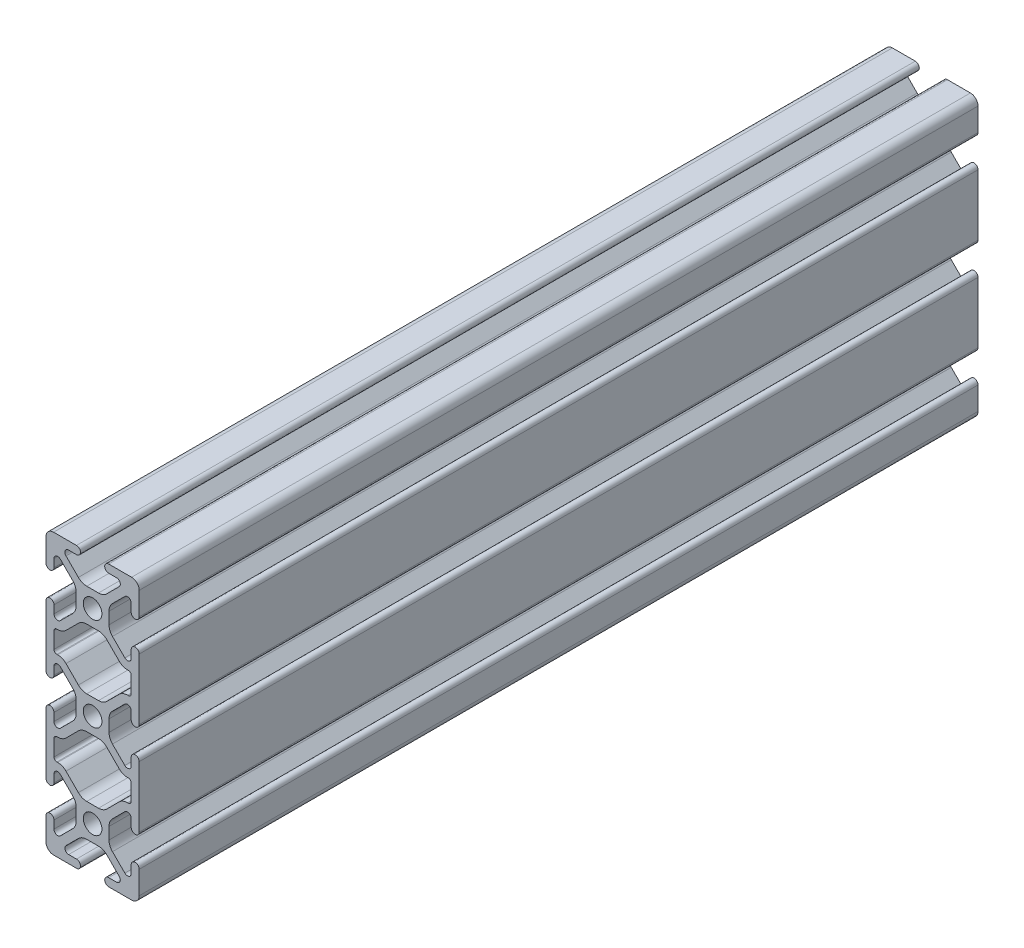
SolidWorks part; units mm, degrees
ref_plane "Front Plane" through (0, 0, 0) normal (0, 0, 1) x (1, 0, 0)
ref_plane "Top Plane" through (0, 0, 0) normal (0, 1, 0) x (1, 0, 0)
ref_plane "Right Plane" through (0, 0, 0) normal (1, 0, 0) x (0, 0, -1)
ref_plane "Plane1" through (0, 0, -225) normal (0, 0, -1) x (-1, 0, 0)
sketch "Sketch1" plane through (0, 0, -225) normal (0, 0, -1) x (-1, 0, 0)
  line L0 (10.36, -10.33) -> (10.36, -14.67)
  line L1 (9.6, -15.43) -> (9.3582, -15.43)
  line L2 (7.1366, -16.3502) -> (3.8153, -19.6715)
  line L3 (1.5737, -20.6) -> (-1.5737, -20.6)
  line L4 (-3.8153, -19.6715) -> (-7.1366, -16.3502)
  line L5 (-9.3582, -15.43) -> (-9.6, -15.43)
  line L6 (-10.36, -14.67) -> (-10.36, -10.33)
  line L7 (-9.6, -9.57) -> (-9.3582, -9.57)
  line L8 (-7.1366, -8.6498) -> (-3.8153, -5.3285)
  line L9 (-1.5737, -4.4) -> (1.5737, -4.4)
  line L10 (3.8153, -5.3285) -> (7.1366, -8.6498)
  line L11 (9.3582, -9.57) -> (9.6, -9.57)
  line L12 (10.36, 14.67) -> (10.36, 10.33)
  line L13 (9.6, 9.57) -> (9.3582, 9.57)
  line L14 (7.1366, 8.6498) -> (3.8153, 5.3285)
  line L15 (1.5737, 4.4) -> (-1.5737, 4.4)
  line L16 (-3.8153, 5.3285) -> (-7.1366, 8.6498)
  line L17 (-9.3582, 9.57) -> (-9.6, 9.57)
  line L18 (-10.36, 10.33) -> (-10.36, 14.67)
  line L19 (-9.6, 15.43) -> (-9.3582, 15.43)
  line L20 (-7.1366, 16.3502) -> (-3.8153, 19.6715)
  line L21 (-1.5737, 20.6) -> (1.5737, 20.6)
  line L22 (3.8153, 19.6715) -> (7.1366, 16.3502)
  line L23 (9.3582, 15.43) -> (9.6, 15.43)
  line L24 (10.36, -29.32) -> (10.36, -31.4282)
  line L25 (8.6498, -32.1366) -> (5.3285, -28.8153)
  line L26 (4.4, -26.5737) -> (4.4, -23.4263)
  line L27 (5.3285, -21.1847) -> (8.6498, -17.8634)
  line L28 (10.36, -18.5718) -> (10.36, -20.68)
  line L29 (12.5, -20.68) -> (12.5, -4.32)
  line L30 (10.36, -4.32) -> (10.36, -6.4282)
  line L31 (8.6498, -7.1366) -> (5.3285, -3.8153)
  line L32 (4.4, -1.5737) -> (4.4, 1.5737)
  line L33 (5.3285, 3.8153) -> (8.6498, 7.1366)
  line L34 (10.36, 6.4282) -> (10.36, 4.32)
  line L35 (12.5, 4.32) -> (12.5, 20.68)
  line L36 (10.36, 20.68) -> (10.36, 18.5718)
  line L37 (8.6498, 17.8634) -> (5.3285, 21.1847)
  line L38 (4.4, 23.4263) -> (4.4, 26.5737)
  line L39 (5.3285, 28.8153) -> (8.6498, 32.1366)
  line L40 (10.36, 31.4282) -> (10.36, 29.32)
  line L41 (12.5, 29.32) -> (12.5, 35.469)
  line L42 (10.469, 37.5) -> (4.32, 37.5)
  line L43 (4.32, 35.36) -> (6.4282, 35.36)
  line L44 (7.1366, 33.6498) -> (3.8153, 30.3285)
  line L45 (1.5737, 29.4) -> (-1.5737, 29.4)
  line L46 (-3.8153, 30.3285) -> (-7.1366, 33.6498)
  line L47 (-6.4282, 35.36) -> (-4.32, 35.36)
  line L48 (-4.32, 37.5) -> (-10.469, 37.5)
  line L49 (-12.5, 35.469) -> (-12.5, 29.32)
  line L50 (-10.36, 29.32) -> (-10.36, 31.4282)
  line L51 (-8.6498, 32.1366) -> (-5.3285, 28.8153)
  line L52 (-4.4, 26.5737) -> (-4.4, 23.4263)
  line L53 (-5.3285, 21.1847) -> (-8.6498, 17.8634)
  line L54 (-10.36, 18.5718) -> (-10.36, 20.68)
  line L55 (-12.5, 20.68) -> (-12.5, 4.32)
  line L56 (-10.36, 4.32) -> (-10.36, 6.4282)
  line L57 (-8.6498, 7.1366) -> (-5.3285, 3.8153)
  line L58 (-4.4, 1.5737) -> (-4.4, -1.5737)
  line L59 (-5.3285, -3.8153) -> (-8.6498, -7.1366)
  line L60 (-10.36, -6.4282) -> (-10.36, -4.32)
  line L61 (-12.5, -4.32) -> (-12.5, -20.68)
  line L62 (-10.36, -20.68) -> (-10.36, -18.5718)
  line L63 (-8.6498, -17.8634) -> (-5.3285, -21.1847)
  line L64 (-4.4, -23.4263) -> (-4.4, -26.5737)
  line L65 (-5.3285, -28.8153) -> (-8.6498, -32.1366)
  line L66 (-10.36, -31.4282) -> (-10.36, -29.32)
  line L67 (-12.5, -29.32) -> (-12.5, -35.469)
  line L68 (-10.469, -37.5) -> (-4.32, -37.5)
  line L69 (-4.32, -35.36) -> (-6.4282, -35.36)
  line L70 (-7.1366, -33.6498) -> (-3.8153, -30.3285)
  line L71 (-1.5737, -29.4) -> (1.5737, -29.4)
  line L72 (3.8153, -30.3285) -> (7.1366, -33.6498)
  line L73 (6.4282, -35.36) -> (4.32, -35.36)
  line L74 (4.32, -37.5) -> (10.469, -37.5)
  line L75 (12.5, -35.469) -> (12.5, -29.32)
  arc A0 (9.6, -9.57) -> (10.36, -10.33) centre (9.6, -10.33) cw
  arc A1 (10.36, -14.67) -> (9.6, -15.43) centre (9.6, -14.67) cw
  arc A2 (9.3582, -15.43) -> (7.1366, -16.3502) centre (9.3582, -18.5718) ccw
  arc A3 (3.8153, -19.6715) -> (1.5737, -20.6) centre (1.5737, -17.43) cw
  arc A4 (-1.5737, -20.6) -> (-3.8153, -19.6715) centre (-1.5737, -17.43) cw
  arc A5 (-7.1366, -16.3502) -> (-9.3582, -15.43) centre (-9.3582, -18.5718) ccw
  arc A6 (-9.6, -15.43) -> (-10.36, -14.67) centre (-9.6, -14.67) cw
  arc A7 (-10.36, -10.33) -> (-9.6, -9.57) centre (-9.6, -10.33) cw
  arc A8 (-9.3582, -9.57) -> (-7.1366, -8.6498) centre (-9.3582, -6.4282) ccw
  arc A9 (-3.8153, -5.3285) -> (-1.5737, -4.4) centre (-1.5737, -7.57) cw
  arc A10 (1.5737, -4.4) -> (3.8153, -5.3285) centre (1.5737, -7.57) cw
  arc A11 (7.1366, -8.6498) -> (9.3582, -9.57) centre (9.3582, -6.4282) ccw
  arc A12 (10.36, 10.33) -> (9.6, 9.57) centre (9.6, 10.33) cw
  arc A13 (9.3582, 9.57) -> (7.1366, 8.6498) centre (9.3582, 6.4282) ccw
  arc A14 (3.8153, 5.3285) -> (1.5737, 4.4) centre (1.5737, 7.57) cw
  arc A15 (-1.5737, 4.4) -> (-3.8153, 5.3285) centre (-1.5737, 7.57) cw
  arc A16 (-7.1366, 8.6498) -> (-9.3582, 9.57) centre (-9.3582, 6.4282) ccw
  arc A17 (-9.6, 9.57) -> (-10.36, 10.33) centre (-9.6, 10.33) cw
  arc A18 (-10.36, 14.67) -> (-9.6, 15.43) centre (-9.6, 14.67) cw
  arc A19 (-9.3582, 15.43) -> (-7.1366, 16.3502) centre (-9.3582, 18.5718) ccw
  arc A20 (-3.8153, 19.6715) -> (-1.5737, 20.6) centre (-1.5737, 17.43) cw
  arc A21 (1.5737, 20.6) -> (3.8153, 19.6715) centre (1.5737, 17.43) cw
  arc A22 (7.1366, 16.3502) -> (9.3582, 15.43) centre (9.3582, 18.5718) ccw
  arc A23 (9.6, 15.43) -> (10.36, 14.67) centre (9.6, 14.67) cw
  circle A24 centre (0, -25) radius 2.5
  circle A25 centre (0, 25) radius 2.5
  circle A26 centre (0, 0) radius 2.5
  arc A27 (12.5, -29.32) -> (10.36, -29.32) centre (11.43, -29.32) ccw
  arc A28 (10.36, -31.4282) -> (8.6498, -32.1366) centre (9.3582, -31.4282) cw
  arc A29 (5.3285, -28.8153) -> (4.4, -26.5737) centre (7.57, -26.5737) cw
  arc A30 (4.4, -23.4263) -> (5.3285, -21.1847) centre (7.57, -23.4263) cw
  arc A31 (8.6498, -17.8634) -> (10.36, -18.5718) centre (9.3582, -18.5718) cw
  arc A32 (10.36, -20.68) -> (12.5, -20.68) centre (11.43, -20.68) ccw
  arc A33 (12.5, -4.32) -> (10.36, -4.32) centre (11.43, -4.32) ccw
  arc A34 (10.36, -6.4282) -> (8.6498, -7.1366) centre (9.3582, -6.4282) cw
  arc A35 (5.3285, -3.8153) -> (4.4, -1.5737) centre (7.57, -1.5737) cw
  arc A36 (4.4, 1.5737) -> (5.3285, 3.8153) centre (7.57, 1.5737) cw
  arc A37 (8.6498, 7.1366) -> (10.36, 6.4282) centre (9.3582, 6.4282) cw
  arc A38 (10.36, 4.32) -> (12.5, 4.32) centre (11.43, 4.32) ccw
  arc A39 (12.5, 20.68) -> (10.36, 20.68) centre (11.43, 20.68) ccw
  arc A40 (10.36, 18.5718) -> (8.6498, 17.8634) centre (9.3582, 18.5718) cw
  arc A41 (5.3285, 21.1847) -> (4.4, 23.4263) centre (7.57, 23.4263) cw
  arc A42 (4.4, 26.5737) -> (5.3285, 28.8153) centre (7.57, 26.5737) cw
  arc A43 (8.6498, 32.1366) -> (10.36, 31.4282) centre (9.3582, 31.4282) cw
  arc A44 (10.36, 29.32) -> (12.5, 29.32) centre (11.43, 29.32) ccw
  arc A45 (12.5, 35.469) -> (10.469, 37.5) centre (10.469, 35.469) ccw
  arc A46 (4.32, 37.5) -> (4.32, 35.36) centre (4.32, 36.43) ccw
  arc A47 (6.4282, 35.36) -> (7.1366, 33.6498) centre (6.4282, 34.3582) cw
  arc A48 (3.8153, 30.3285) -> (1.5737, 29.4) centre (1.5737, 32.57) cw
  arc A49 (-1.5737, 29.4) -> (-3.8153, 30.3285) centre (-1.5737, 32.57) cw
  arc A50 (-7.1366, 33.6498) -> (-6.4282, 35.36) centre (-6.4282, 34.3582) cw
  arc A51 (-4.32, 35.36) -> (-4.32, 37.5) centre (-4.32, 36.43) ccw
  arc A52 (-10.469, 37.5) -> (-12.5, 35.469) centre (-10.469, 35.469) ccw
  arc A53 (-12.5, 29.32) -> (-10.36, 29.32) centre (-11.43, 29.32) ccw
  arc A54 (-10.36, 31.4282) -> (-8.6498, 32.1366) centre (-9.3582, 31.4282) cw
  arc A55 (-5.3285, 28.8153) -> (-4.4, 26.5737) centre (-7.57, 26.5737) cw
  arc A56 (-4.4, 23.4263) -> (-5.3285, 21.1847) centre (-7.57, 23.4263) cw
  arc A57 (-8.6498, 17.8634) -> (-10.36, 18.5718) centre (-9.3582, 18.5718) cw
  arc A58 (-10.36, 20.68) -> (-12.5, 20.68) centre (-11.43, 20.68) ccw
  arc A59 (-12.5, 4.32) -> (-10.36, 4.32) centre (-11.43, 4.32) ccw
  arc A60 (-10.36, 6.4282) -> (-8.6498, 7.1366) centre (-9.3582, 6.4282) cw
  arc A61 (-5.3285, 3.8153) -> (-4.4, 1.5737) centre (-7.57, 1.5737) cw
  arc A62 (-4.4, -1.5737) -> (-5.3285, -3.8153) centre (-7.57, -1.5737) cw
  arc A63 (-8.6498, -7.1366) -> (-10.36, -6.4282) centre (-9.3582, -6.4282) cw
  arc A64 (-10.36, -4.32) -> (-12.5, -4.32) centre (-11.43, -4.32) ccw
  arc A65 (-12.5, -20.68) -> (-10.36, -20.68) centre (-11.43, -20.68) ccw
  arc A66 (-10.36, -18.5718) -> (-8.6498, -17.8634) centre (-9.3582, -18.5718) cw
  arc A67 (-5.3285, -21.1847) -> (-4.4, -23.4263) centre (-7.57, -23.4263) cw
  arc A68 (-4.4, -26.5737) -> (-5.3285, -28.8153) centre (-7.57, -26.5737) cw
  arc A69 (-8.6498, -32.1366) -> (-10.36, -31.4282) centre (-9.3582, -31.4282) cw
  arc A70 (-10.36, -29.32) -> (-12.5, -29.32) centre (-11.43, -29.32) ccw
  arc A71 (-12.5, -35.469) -> (-10.469, -37.5) centre (-10.469, -35.469) ccw
  arc A72 (-4.32, -37.5) -> (-4.32, -35.36) centre (-4.32, -36.43) ccw
  arc A73 (-6.4282, -35.36) -> (-7.1366, -33.6498) centre (-6.4282, -34.3582) cw
  arc A74 (-3.8153, -30.3285) -> (-1.5737, -29.4) centre (-1.5737, -32.57) cw
  arc A75 (1.5737, -29.4) -> (3.8153, -30.3285) centre (1.5737, -32.57) cw
  arc A76 (7.1366, -33.6498) -> (6.4282, -35.36) centre (6.4282, -34.3582) cw
  arc A77 (4.32, -35.36) -> (4.32, -37.5) centre (4.32, -36.43) ccw
  arc A78 (10.469, -37.5) -> (12.5, -35.469) centre (10.469, -35.469) ccw
extrude "Boss-Extrude1" add sketch "Sketch1" against normal blind 225
